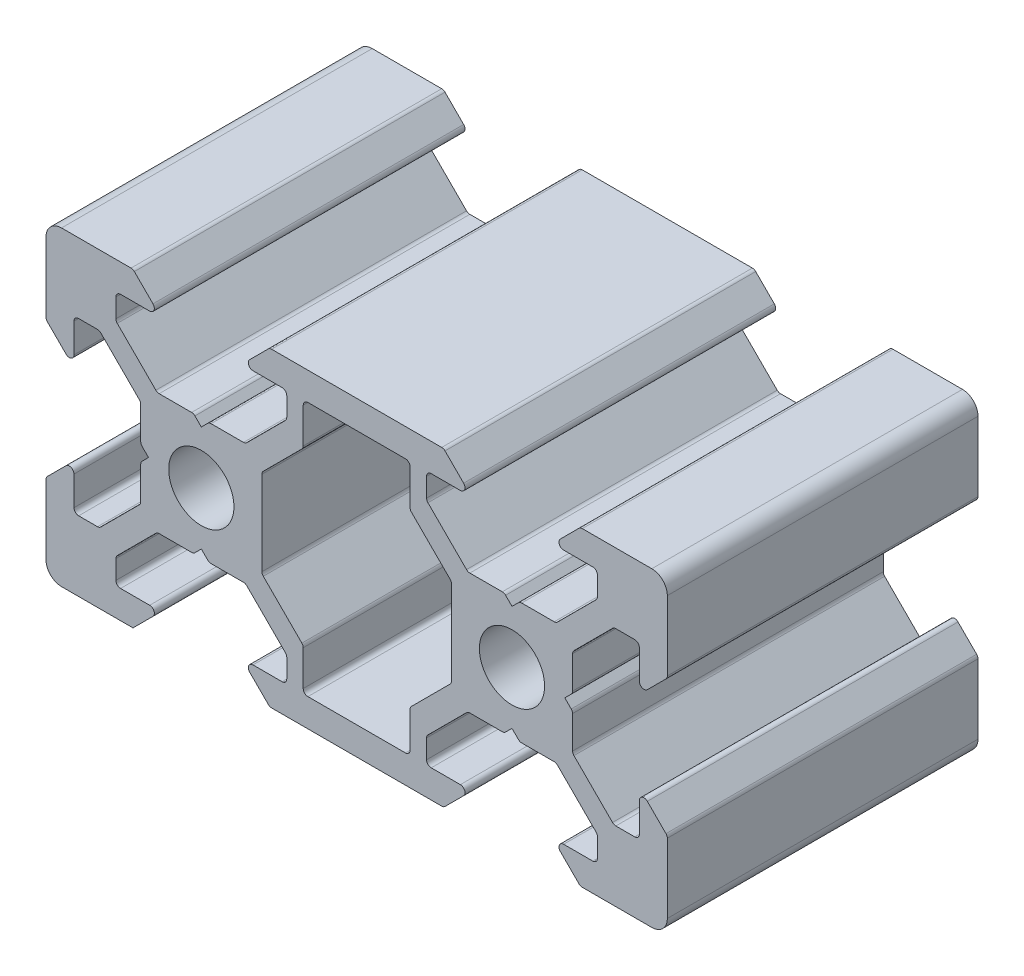
SolidWorks part; units mm, degrees
material "АД31Т ГОСТ 4784-97"
ref_plane "Спереди" through (0, 0, 0) normal (0, 0, 1) x (1, 0, 0)
ref_plane "Сверху" through (0, 0, 0) normal (0, 1, 0) x (1, 0, 0)
ref_plane "Справа" through (0, 0, 0) normal (1, 0, 0) x (0, 0, -1)
sketch "Эскиз1" plane through (0, 0, 0) normal (0, 0, 1) x (1, 0, 0)
  line L0 (12.9654, 0) -> (-12.9654, 0) construction
  line L1 (0, -12.9654) -> (0, 12.9654) construction
  line L2 (0, 0) -> (-18.3359, -18.3359) construction
  line L3 (-10, -10) -> (-10, -4.4)
  line L4 (-10, -4.4) -> (-8.2, -2.6)
  line L5 (-8.2, -2.6) -> (-8.2, -5.4993)
  line L6 (-8.2, -5.4993) -> (-6.56, -5.4993)
  line L7 (-6.56, -5.4993) -> (-3.9007, -2.84)
  line L8 (-3.9007, -2.84) -> (-3.9007, -0.5)
  line L9 (-3.9007, -0.5) -> (-3.4007, 0)
  line L10 (-0.5, -3.9007) -> (0, -3.4007)
  line L11 (-2.84, -3.9007) -> (-0.5, -3.9007)
  line L12 (-5.4993, -6.56) -> (-2.84, -3.9007)
  line L13 (-5.4993, -8.2) -> (-5.4993, -6.56)
  line L14 (-2.6, -8.2) -> (-5.4993, -8.2)
  line L15 (-4.4, -10) -> (-2.6, -8.2)
  line L16 (-10, -10) -> (-4.4, -10)
  line L17 (-10, 10) -> (-4.4, 10)
  line L18 (-4.4, 10) -> (-2.6, 8.2)
  line L19 (-2.6, 8.2) -> (-5.4993, 8.2)
  line L20 (-5.4993, 8.2) -> (-5.4993, 6.56)
  line L21 (-5.4993, 6.56) -> (-2.84, 3.9007)
  line L22 (-2.84, 3.9007) -> (-0.5, 3.9007)
  line L23 (-0.5, 3.9007) -> (0, 3.4007)
  line L24 (-3.9007, 0.5) -> (-3.4007, 0)
  line L25 (-3.9007, 2.84) -> (-3.9007, 0.5)
  line L26 (-6.56, 5.4993) -> (-3.9007, 2.84)
  line L27 (-8.2, 5.4993) -> (-6.56, 5.4993)
  line L28 (-8.2, 2.6) -> (-8.2, 5.4993)
  line L29 (-10, 4.4) -> (-8.2, 2.6)
  line L30 (-10, 10) -> (-10, 4.4)
  line L31 (0.5, 3.9007) -> (0, 3.4007)
  line L32 (0.5, -3.9007) -> (0, -3.4007)
  line L33 (10, -10) -> (10, 10) construction
  line L34 (3.9007, -0.5) -> (3.9007, 0.5)
  line L35 (6.56, -5.4993) -> (6.56, -8.2)
  line L36 (13.44, -5.4993) -> (16.0993, -2.84)
  line L37 (6.56, 5.4993) -> (3.9007, 2.84)
  line L38 (3.9007, 2.84) -> (3.9007, 0.5)
  line L39 (6.56, -8.2) -> (13.44, -8.2)
  line L40 (2.84, 3.9007) -> (0.5, 3.9007)
  line L41 (5.4993, 6.56) -> (2.84, 3.9007)
  line L42 (5.4993, 8.2) -> (5.4993, 6.56)
  line L43 (2.6, 8.2) -> (5.4993, 8.2)
  line L44 (4.4, 10) -> (2.6, 8.2)
  line L45 (15.6, 10) -> (4.4, 10)
  line L46 (15.6, -10) -> (4.4, -10)
  line L47 (4.4, -10) -> (2.6, -8.2)
  line L48 (2.6, -8.2) -> (5.4993, -8.2)
  line L49 (5.4993, -8.2) -> (5.4993, -6.56)
  line L50 (5.4993, -6.56) -> (2.84, -3.9007)
  line L51 (2.84, -3.9007) -> (0.5, -3.9007)
  line L52 (6.56, 5.4993) -> (6.56, 8.2)
  line L53 (3.9007, -2.84) -> (3.9007, -0.5)
  line L54 (6.56, -5.4993) -> (3.9007, -2.84)
  line L55 (16.0993, -2.84) -> (16.0993, -0.5)
  line L56 (6.56, 8.2) -> (13.44, 8.2)
  line L57 (13.44, 5.4993) -> (13.44, 8.2)
  line L58 (17.16, -3.9007) -> (19.5, -3.9007)
  line L59 (14.5007, -6.56) -> (17.16, -3.9007)
  line L60 (14.5007, -8.2) -> (14.5007, -6.56)
  line L61 (17.4, -8.2) -> (14.5007, -8.2)
  line L62 (15.6, -10) -> (17.4, -8.2)
  line L63 (15.6, 10) -> (17.4, 8.2)
  line L64 (17.4, 8.2) -> (14.5007, 8.2)
  line L65 (14.5007, 8.2) -> (14.5007, 6.56)
  line L66 (14.5007, 6.56) -> (17.16, 3.9007)
  line L67 (17.16, 3.9007) -> (19.5, 3.9007)
  line L68 (16.0993, 2.84) -> (16.0993, 0.5)
  line L69 (13.44, 5.4993) -> (16.0993, 2.84)
  line L70 (13.44, -5.4993) -> (13.44, -8.2)
  line L71 (16.0993, -0.5) -> (16.0993, 0.5)
  line L72 (19.5, -3.9007) -> (20, -3.4007)
  line L73 (19.5, 3.9007) -> (20, 3.4007)
  line L74 (30, 10) -> (30, 4.4)
  line L75 (30, 4.4) -> (28.2, 2.6)
  line L76 (28.2, 2.6) -> (28.2, 5.4993)
  line L77 (28.2, 5.4993) -> (26.56, 5.4993)
  line L78 (26.56, 5.4993) -> (23.9007, 2.84)
  line L79 (23.9007, 2.84) -> (23.9007, 0.5)
  line L80 (23.9007, 0.5) -> (23.4007, 0)
  line L81 (20.5, 3.9007) -> (20, 3.4007)
  line L82 (22.84, 3.9007) -> (20.5, 3.9007)
  line L83 (25.4993, 6.56) -> (22.84, 3.9007)
  line L84 (25.4993, 8.2) -> (25.4993, 6.56)
  line L85 (22.6, 8.2) -> (25.4993, 8.2)
  line L86 (24.4, 10) -> (22.6, 8.2)
  line L87 (30, 10) -> (24.4, 10)
  line L88 (30, -10) -> (24.4, -10)
  line L89 (24.4, -10) -> (22.6, -8.2)
  line L90 (22.6, -8.2) -> (25.4993, -8.2)
  line L91 (25.4993, -8.2) -> (25.4993, -6.56)
  line L92 (25.4993, -6.56) -> (22.84, -3.9007)
  line L93 (22.84, -3.9007) -> (20.5, -3.9007)
  line L94 (20.5, -3.9007) -> (20, -3.4007)
  line L95 (23.9007, -0.5) -> (23.4007, 0)
  line L96 (23.9007, -2.84) -> (23.9007, -0.5)
  line L97 (26.56, -5.4993) -> (23.9007, -2.84)
  line L98 (28.2, -5.4993) -> (26.56, -5.4993)
  line L99 (28.2, -2.6) -> (28.2, -5.4993)
  line L100 (30, -4.4) -> (28.2, -2.6)
  line L101 (30, -10) -> (30, -4.4)
  circle A0 centre (0, 0) radius 2.1
  circle A1 centre (20, 0) radius 2.1
  point P62 (10, 8.2)
  point P80 (10, -8.2)
  dimension "D5" = 2.6
  dimension "D10" = 4.2
  dimension "D2" = 10
  dimension "D3" = 1.64
  dimension "D4" = 1.5
  dimension "D6" = 1.8
  dimension "D7" = 2.84
  dimension "D8" = 0.5
  dimension "D9" = 45
extrude "Бобышка-Вытянуть1" add sketch "Эскиз1" along normal blind 20
fillet "Скругление1" radius 1 4 edges at (-10, 10, 10) (-10, -10, 10) (30, 10, 10) (30, -10, 10)
fillet "Скругление2" radius 0.3 83 edges at (-4.4, 10, 10) (-2.6, 8.2, 10) (-5.4993, 8.2, 10) (-5.4993, 6.56, 10) (-2.84, 3.9007, 10) (-0.5, 3.9007, 10) (0.5, 3.9007, 10) (2.84, 3.9007, 10) (5.4993, 6.56, 10) (4.4, 10, 10) (5.4993, 8.2, 10) (2.6, 8.2, 10) (3.9007, 2.84, 10) (3.9007, -2.84, 10) (4.4, -10, 10) (2.6, -8.2, 10) (5.4993, -8.2, 10) (5.4993, -6.56, 10) (2.84, -3.9007, 10) (0.5, -3.9007, 10) (-0.5, -3.9007, 10) (-2.84, -3.9007, 10) (-5.4993, -6.56, 10) (-5.4993, -8.2, 10) (-2.6, -8.2, 10) (-10, -4.4, 10) (-8.2, -2.6, 10) (-8.2, -5.4993, 10) (-6.56, -5.4993, 10) (-3.9007, -2.84, 10) (-3.9007, -0.5, 10) (-3.9007, 0.5, 10) (-3.9007, 2.84, 10) (-6.56, 5.4993, 10) (-8.2, 5.4993, 10) (-8.2, 2.6, 10) (-10, 4.4, 10) (6.56, -5.4993, 10) (6.56, 5.4993, 10) (6.56, 8.2, 10) (13.44, 8.2, 10) (13.44, 5.4993, 10) (16.0993, 2.84, 10) (16.0993, -2.84, 10) (13.44, -5.4993, 10) (13.44, -8.2, 10) (6.56, -8.2, 10) (15.6, 10, 10) (17.4, 8.2, 10) (14.5007, 8.2, 10) (14.5007, 6.56, 10) (17.16, 3.9007, 10) (19.5, 3.9007, 10) (20.5, 3.9007, 10) (22.84, 3.9007, 10) (25.4993, 6.56, 10) (25.4993, 8.2, 10) (22.6, 8.2, 10) (24.4, 10, 10) (30, 4.4, 10) (28.2, 2.6, 10) (28.2, 5.4993, 10) (26.56, 5.4993, 10) (23.9007, 2.84, 10) (23.9007, 0.5, 10) (23.9007, -0.5, 10) (23.9007, -2.84, 10) (26.56, -5.4993, 10) (28.2, -5.4993, 10) (28.2, -2.6, 10) (30, -4.4, 10) (24.4, -10, 10) (22.6, -8.2, 10) (25.4993, -8.2, 10) (25.4993, -6.56, 10) (22.84, -3.9007, 10) (20.5, -3.9007, 10) (19.5, -3.9007, 10) (17.16, -3.9007, 10) (14.5007, -6.56, 10) (14.5007, -8.2, 10) (17.4, -8.2, 10) (15.6, -10, 10)
